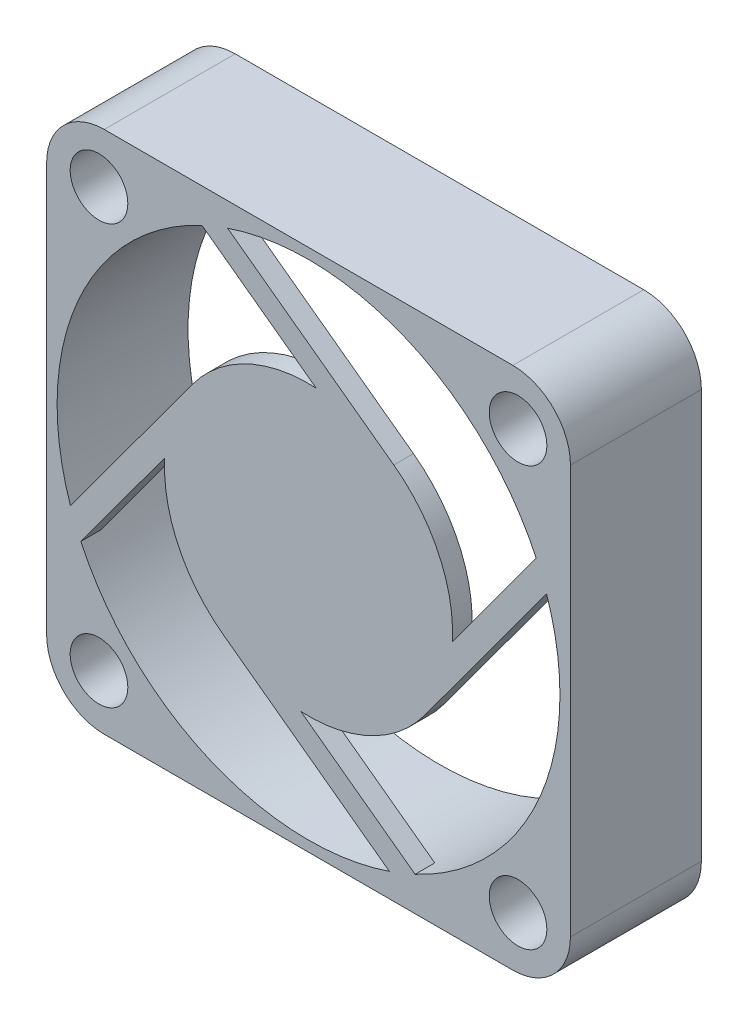
SolidWorks part; units mm, degrees
ref_plane "Front Plane" through (0, 0, 0) normal (0, 0, 1) x (1, 0, 0)
ref_plane "Top Plane" through (0, 0, 0) normal (0, 1, 0) x (1, 0, 0)
ref_plane "Right Plane" through (0, 0, 0) normal (1, 0, 0) x (0, 0, -1)
sketch "Sketch1" plane through (0, 0, 0) normal (0, 0, 1) x (1, 0, 0)
  line L1 (20, 20) -> (-20, 20)
  line L2 (20, 20) -> (20, -20)
  line L3 (20, -20) -> (-20, -20)
  line L4 (-20, 20) -> (-20, -20)
  line L5 (20, 20) -> (-20, -20) construction
  line L6 (20, -20) -> (-20, 20) construction
  point P0 (0, 0)
extrude "Boss-Extrude1" add sketch "Sketch1" along normal blind 10
sketch "Sketch2" plane through (0, 0, 10) normal (0, 0, 1) x (1, 0, 0)
  line L8 (-16, 16) -> (-16, -16)
  line L9 (-16, -16) -> (16, -16)
  line L10 (16, -16) -> (16, 16)
  line L11 (16, 16) -> (-16, 16)
  line L12 (-16, 16) -> (-16, -16) construction
  line L13 (-16, -16) -> (16, -16) construction
  line L14 (16, -16) -> (16, 16) construction
  line L15 (16, 16) -> (-16, 16) construction
  circle A0 centre (-16, 16) radius 2.2
  circle A1 centre (16, 16) radius 2.2
  circle A2 centre (16, -16) radius 2.2
  circle A3 centre (-16, -16) radius 2.2
  dimension "D1" = 4
extrude "Cut-Extrude1" cut sketch "Sketch2" against normal blind 10
sketch "Sketch3" plane through (0, 0, 10) normal (0, 0, 1) x (1, 0, 0)
  line L0 (0, 20) -> (0, -20) construction
  line L1 (20, 20) -> (-20, 20) construction
  line L2 (-20, -20) -> (20, -20) construction
  circle A0 centre (0, 0) radius 19.2
extrude "Cut-Extrude2" cut sketch "Sketch3" against normal blind 10
fillet "Fillet1" radius 4.4 4 edges at (20, -20, 5) (-20, -20, 5) (-20, 20, 5) (20, 20, 5)
sketch "Sketch4" plane through (0, 0, 10) normal (0, 0, 1) x (1, 0, 0)
  line L0 (6.5098, 8.8669) -> (-6.1752, 18.1798)
  line L1 (8.8669, -6.5098) -> (18.1798, 6.1752)
  line L2 (-6.5098, -8.8669) -> (6.1752, -18.1798)
  line L3 (-8.8669, 6.5098) -> (-18.1798, -6.1752)
  line L4 (0.5839, 10.9845) -> (-8.1398, 17.3892)
  line L5 (10.9845, -0.5839) -> (17.3892, 8.1398)
  line L6 (-0.5839, -10.9845) -> (8.1398, -17.3892)
  line L7 (-10.9845, 0.5839) -> (-17.3892, -8.1398)
  line L8 (5.4446, 7.416) -> (-7.2405, 16.7289) construction
  line L9 (-7.416, 5.4446) -> (-16.7289, -7.2405) construction
  line L10 (-5.4446, -7.416) -> (7.2405, -16.7289) construction
  line L11 (7.416, -5.4446) -> (16.7289, 7.2405) construction
  arc A0 (0.5839, 10.9845) -> (-8.8669, 6.5098) centre (0, 0) ccw
  circle A1 centre (0, 0) radius 19.2 construction
  arc A2 (-18.1798, -6.1752) -> (-17.3892, -8.1398) centre (0, 0) ccw
  arc A3 (-6.1752, 18.1798) -> (-8.1398, 17.3892) centre (0, 0) ccw
  arc A4 (18.1798, 6.1752) -> (17.3892, 8.1398) centre (0, 0) ccw
  arc A5 (6.1752, -18.1798) -> (8.1398, -17.3892) centre (0, 0) ccw
  arc A6 (-10.9845, 0.5839) -> (-6.5098, -8.8669) centre (0, 0) ccw
  arc A7 (-0.5839, -10.9845) -> (8.8669, -6.5098) centre (0, 0) ccw
  arc A8 (10.9845, -0.5839) -> (6.5098, 8.8669) centre (0, 0) ccw
  dimension "D1" = 4
  dimension "D2" = 1.8
  dimension "D3" = 1.8
extrude "Boss-Extrude2" add sketch "Sketch4" against normal blind 1.5
sketch "Sketch5" plane through (0, 0, 10) normal (0, 0, 1) x (1, 0, 0)
  line L0 (0, -20) -> (0, 20)
  line L1 (-15.6, -20) -> (15.6, -20) construction
  line L2 (15.6, 20) -> (-15.6, 20) construction
  line L4 (-20, 15.6) -> (-20, -15.6) construction
  line L5 (-20, 0) -> (20, 0)
  line L6 (20, -15.6) -> (20, 15.6) construction
